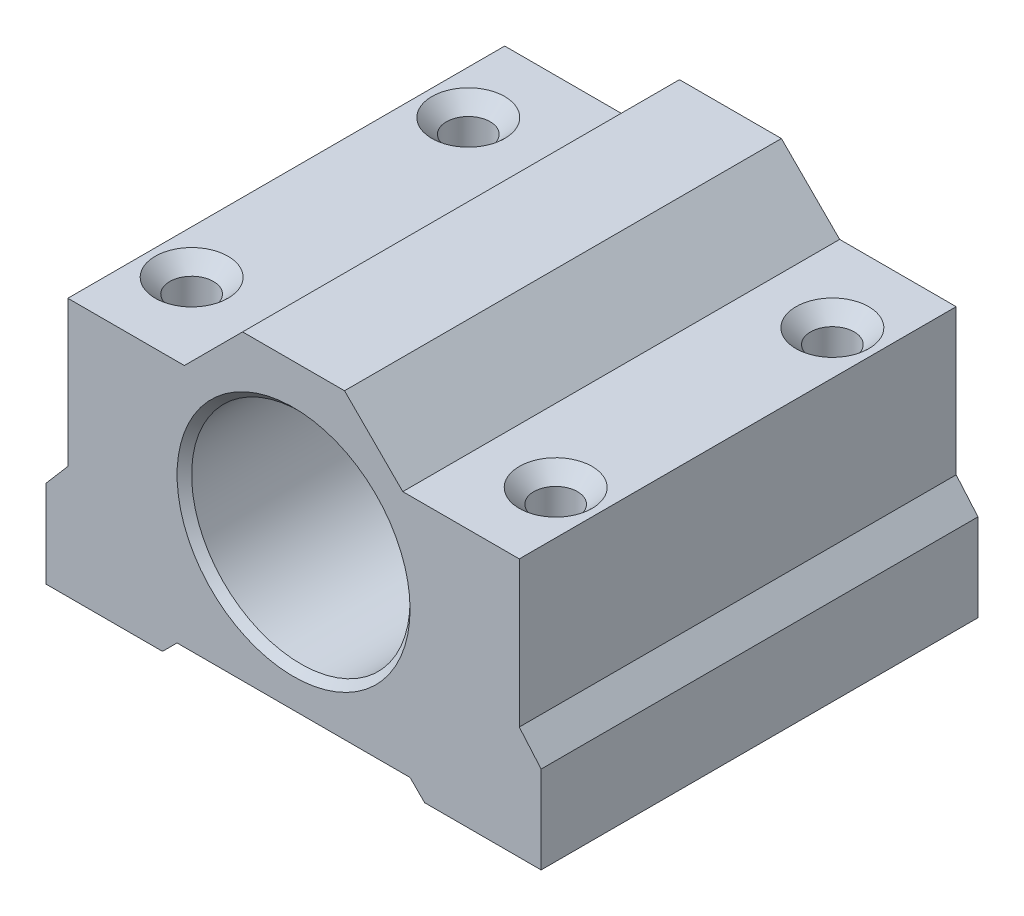
SolidWorks part; units mm, degrees
material "1060 Alloy"
ref_plane "Plane1" through (0, 0, 0) normal (0, 0, 1) x (1, 0, 0)
ref_plane "Plane2" through (0, 0, 0) normal (0, 1, 0) x (1, 0, 0)
ref_plane "Plane3" through (0, 0, 0) normal (1, 0, 0) x (0, 0, -1)
sketch "Sketch1" plane through (0, 0, 0) normal (0, 0, 1) x (1, 0, 0)
  line L0 (0, 0) -> (0, 6)
  line L2 (1.5, 7.75) -> (1.5, 17.75)
  line L3 (1.5, 17.75) -> (9.5, 17.75)
  line L4 (9.5, 17.75) -> (13.5, 21.75)
  line L5 (13.5, 21.75) -> (20.5, 21.75)
  line L13 (25, 1) -> (9, 1)
  line L14 (9, 1) -> (8, 0)
  line L15 (8, 0) -> (0, 0)
  line L16 (0, 6) -> (1.5, 7.75)
  line L18 (17, 14.8773) -> (17, -1.3922) construction
  line L19 (34, 6) -> (32.5, 7.75)
  line L20 (26, 0) -> (34, 0)
  line L21 (25, 1) -> (26, 0)
  line L22 (24.5, 17.75) -> (20.5, 21.75)
  line L23 (32.5, 17.75) -> (24.5, 17.75)
  line L24 (32.5, 7.75) -> (32.5, 17.75)
  line L25 (34, 0) -> (34, 6)
  point P14 (17, 1)
  point P19 (17, 21.75)
  dimension "D1" = 1.75
  dimension "D2" = 6
  dimension "D3" = 8
  dimension "D5" = 16
  dimension "D6" = 1
  dimension "D7" = 10
  dimension "D8" = 1.5
  dimension "D9" = 8
  dimension "D10" = 4
  dimension "D11" = 4
  dimension "D12" = 1
extrude "Boss-Extrude1" add sketch "Sketch1" along normal blind 30
hole_wizard "CSK for M5 Countersunk Flat Head Screw1" positions "Sketch3" profile "Sketch4" countersink size "M5" standard "ISO" end condition through all
sketch "Sketch3" plane through (0, 0, 30) normal (0, 0, 1) x (1, 0, 0)
  line L0 (9, 1) -> (25, 1) construction
  line L1 (32.5, 7.75) -> (32.5, 17.75) construction
  point P0 (17, 11)
  point P5 (17, 1)
  dimension "D1" = 10
  dimension "D2" = 15.5
sketch "Sketch4" plane through (17, 11, 30) normal (1, 0, 0) x (0, -1, 0)
  line L0 (0, 0) -> (0, 30)
  line L1 (0, 30) -> (7.75, 30)
  line L2 (7.5, 29.75) -> (7.5, 0.5)
  line L3 (7.5, 0.5) -> (8, 0)
  line L5 (8, 0) -> (0, 0)
  line L6 (-7.5, 0.5) -> (-8, 0) construction
  line L7 (7.75, 30) -> (7.5, 29.75)
  line L8 (-7.75, 30) -> (-7.5, 29.75) construction
  line L11 (0, -6.35) -> (0, 107.95) construction
  dimension "Thru Hole Dia." = 15
  dimension "Thru Hole Depth" = 30
  dimension "Near C'Sink Dia." = 16
  dimension "Near C'Sink Angle" = 90
  dimension "Far C'Sink Dia." = 15.5
  dimension "Far C'Sink Angle" = 90
hole_wizard "M5 Tapped Hole5" positions "Sketch18" profile "Sketch19" tap size "M5" standard "ISO" end condition through all
sketch "Sketch18" plane through (0, 0, 0) normal (0, -1, 0) x (-1, 0, 0)
  line L0 (-34, -15) -> (-26, -15) construction
  line L1 (-34, -30) -> (-34, 0) construction
  line L4 (-26, 0) -> (-34, 0) construction
  point P0 (-29.5, -5.5)
  point P12 (-29.5, -24.5)
  dimension "D1" = 4.5
  dimension "D2" = 5.5
sketch "Sketch19" plane through (29.5, 0, 5.5) normal (1, 0, 0) x (0, 0, -1)
  line L0 (0, 0) -> (0, 17.75)
  line L1 (0, 17.75) -> (2.5, 17.75)
  line L2 (1.5, 16.75) -> (1.5, 1)
  line L3 (1.5, 1) -> (2.5, 0)
  line L5 (2.5, 0) -> (0, 0)
  line L6 (-1.5, 1) -> (-2.5, 0) construction
  line L7 (2.5, 17.75) -> (1.5, 16.75)
  line L8 (-2.5, 17.75) -> (-1.5, 16.75) construction
  line L11 (0, -6.35) -> (0, 107.95) construction
  dimension "Thru Tap Drill Dia." = 3
  dimension "Thru Tap Drill Depth" = 17.75
  dimension "Near C'Sink Dia." = 5
  dimension "Near C'Sink Angle" = 90
  dimension "Far C'Sink Dia." = 5
  dimension "Far C'Sink Angle" = 90
cosmetic thread "Hole Thread5" parameters "D1"=6, "D2"=5
cosmetic thread "Hole Thread6" parameters "D1"=6, "D2"=5
hole_wizard "M5 Tapped Hole6" positions "Sketch20" profile "Sketch21" tap size "M5" standard "ISO" end condition through all
sketch "Sketch20" plane through (0, 0, 0) normal (0, -1, 0) x (-1, 0, 0)
  line L0 (0, -15) -> (-8, -15) construction
  line L1 (0, -30) -> (0, 0) construction
  line L2 (-8, -30) -> (-8, 0) construction
  line L4 (0, 0) -> (-8, 0) construction
  point P0 (-4.5, -5.5)
  point P11 (-4.5, -24.5)
  dimension "D1" = 5.5
  dimension "D2" = 4.5
sketch "Sketch21" plane through (4.5, 0, 5.5) normal (1, 0, 0) x (0, 0, -1)
  line L0 (0, 0) -> (0, 17.75)
  line L1 (0, 17.75) -> (2.5, 17.75)
  line L2 (1.5, 16.75) -> (1.5, 1)
  line L3 (1.5, 1) -> (2.5, 0)
  line L5 (2.5, 0) -> (0, 0)
  line L6 (-1.5, 1) -> (-2.5, 0) construction
  line L7 (2.5, 17.75) -> (1.5, 16.75)
  line L8 (-2.5, 17.75) -> (-1.5, 16.75) construction
  line L11 (0, -6.35) -> (0, 107.95) construction
  dimension "Thru Tap Drill Dia." = 3
  dimension "Thru Tap Drill Depth" = 17.75
  dimension "Near C'Sink Dia." = 5
  dimension "Near C'Sink Angle" = 90
  dimension "Far C'Sink Dia." = 5
  dimension "Far C'Sink Angle" = 90
cosmetic thread "Hole Thread7" parameters "D1"=6, "D2"=5
cosmetic thread "Hole Thread8" parameters "D1"=6, "D2"=5
